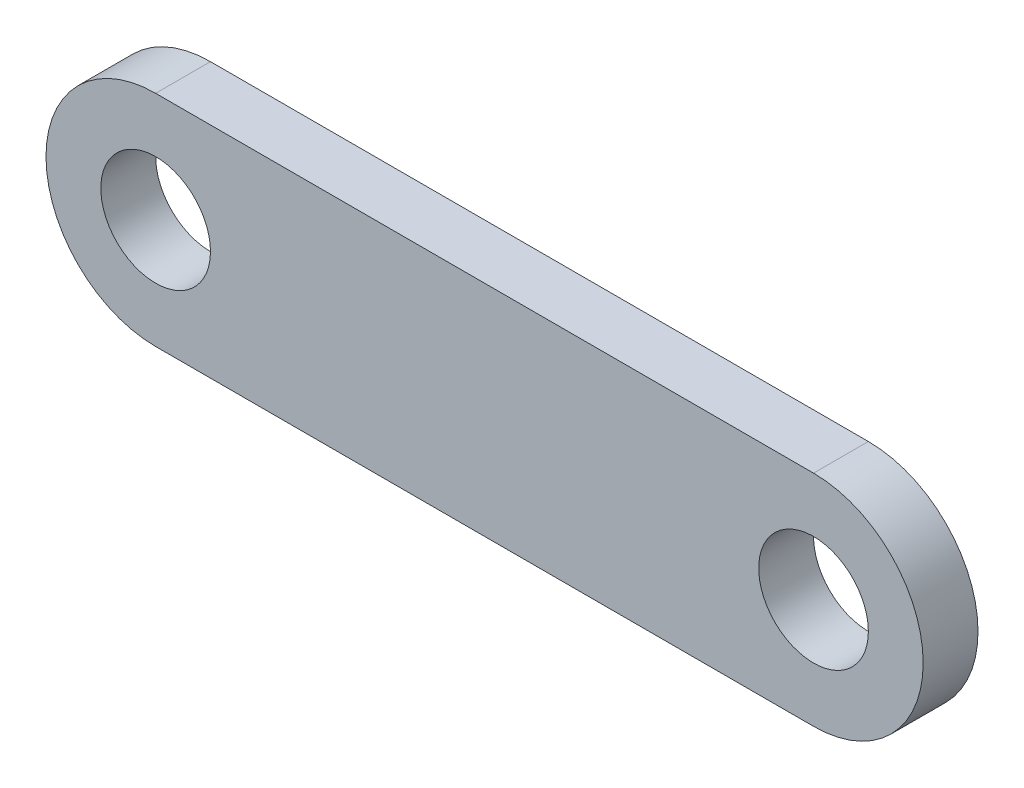
SolidWorks part; units mm, degrees
ref_plane "Спереди" through (0, 0, 0) normal (0, 0, 1) x (1, 0, 0)
ref_plane "Сверху" through (0, 0, 0) normal (0, 1, 0) x (1, 0, 0)
ref_plane "Справа" through (0, 0, 0) normal (1, 0, 0) x (0, 0, -1)
sketch "Эскиз1" plane through (0, 0, 0) normal (0, 0, 1) x (1, 0, 0)
  line L0 (0, 0) -> (60, 0) construction
  line L1 (0, 10) -> (60, 10)
  line L2 (0, -10) -> (60, -10)
  circle A0 centre (0, 0) radius 5
  circle A1 centre (60, 0) radius 5
  arc A2 (0, 10) -> (0, -10) centre (0, 0) ccw
  arc A3 (60, -10) -> (60, 10) centre (60, 0) ccw
  point P5 (30, 0)
  dimension "D1" = 10
  dimension "D2" = 20
  dimension "D3" = 60
extrude "Бобышка-Вытянуть1" add sketch "Эскиз1" along normal blind 5
